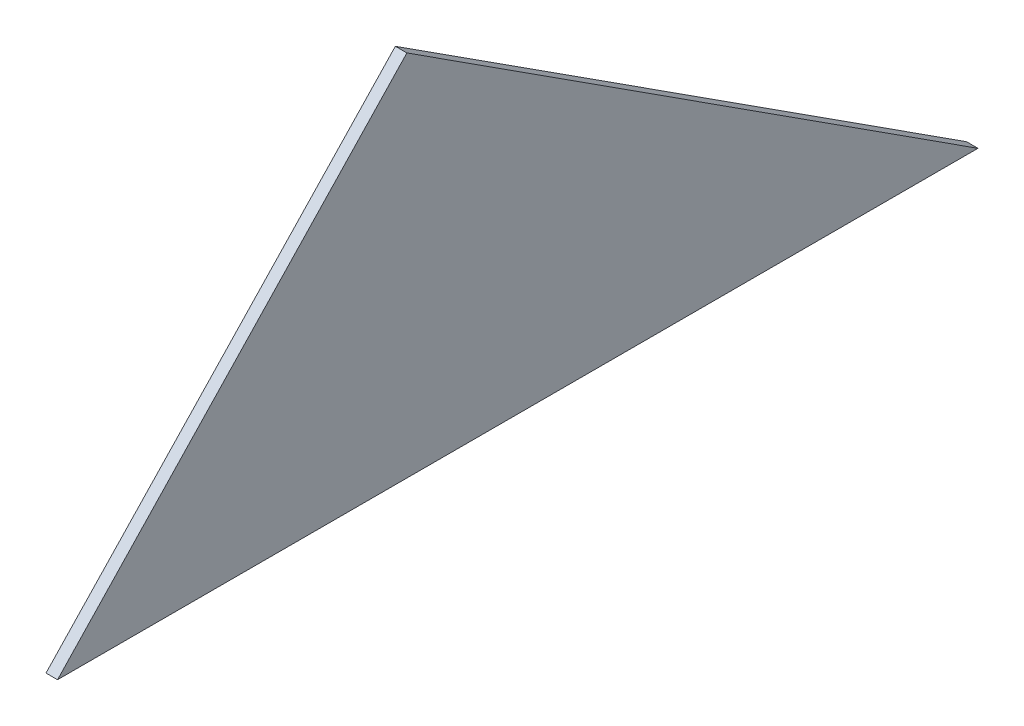
SolidWorks part; units mm, degrees
material "Pine"
ref_plane "Front Plane" through (0, 0, 0) normal (0, 0, 1) x (1, 0, 0)
ref_plane "Top Plane" through (0, 0, 0) normal (0, 1, 0) x (1, 0, 0)
ref_plane "Right Plane" through (0, 0, 0) normal (1, 0, 0) x (0, 0, -1)
sketch "Sketch1" plane through (0, 0, 0) normal (1, 0, 0) x (0, 0, -1)
  line L0 (0, 0) -> (506.73, 0)
  line L5 (506.73, 0) -> (192.3263, 202.6696)
  line L6 (192.3263, 202.6696) -> (0, 0)
  dimension "D1" = 46.5
  dimension "D2" = 279.4
  dimension "D3" = 506.73
extrude "Boss-Extrude1" add sketch "Sketch1" along normal blind 6.35
